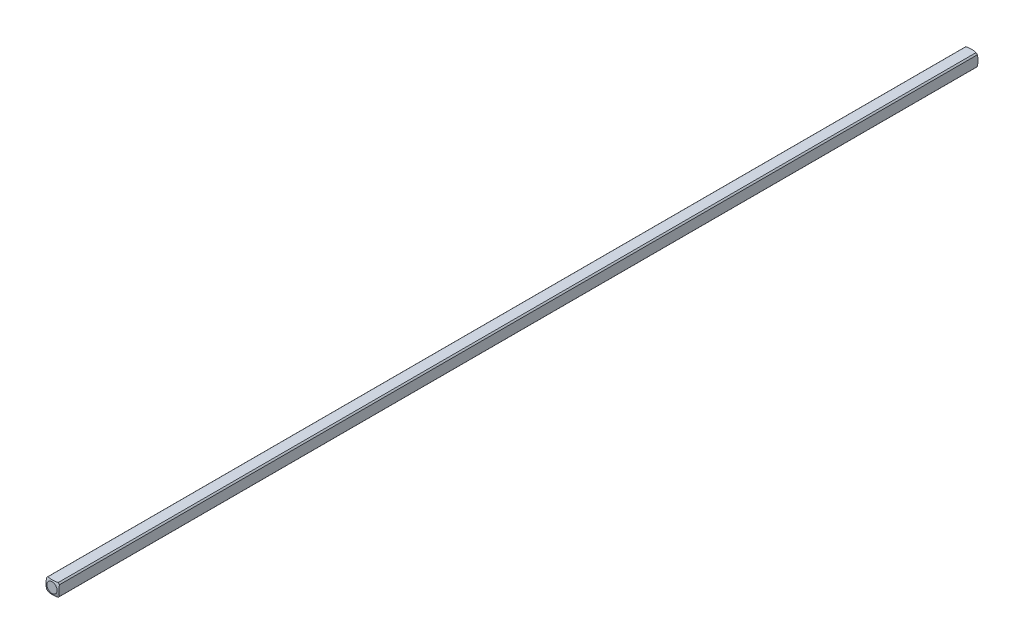
SolidWorks part; units mm, degrees
material "Custom Plastic"
ref_plane "Front Plane" through (0, 0, 0) normal (0, 0, 1) x (1, 0, 0)
ref_plane "Top Plane" through (0, 0, 0) normal (0, 1, 0) x (1, 0, 0)
ref_plane "Right Plane" through (0, 0, 0) normal (1, 0, 0) x (0, 0, -1)
sketch "Sketch1" plane through (0, 0, 0) normal (0, 0, 1) x (1, 0, 0)
  line L0 (-1.5875, -1.5875) -> (1.5875, 1.5875) construction
  line L1 (-1.5875, -1.5875) -> (1.5875, -1.5875)
  line L2 (-1.5875, -1.5875) -> (-1.5875, 1.5875)
  line L3 (-1.5875, 1.5875) -> (1.5875, 1.5875)
  line L4 (1.5875, -1.5875) -> (1.5875, 1.5875)
  dimension "D1" = 3.175
extrude "Boss-Extrude1" add sketch "Sketch1" along normal blind 114.3
sketch "Sketch2" plane through (0, 0, 0) normal (0, 0, -1) x (-1, 0, 0)
  circle A0 centre (0, 0) radius 2.032
  dimension "D1" = 4.064
extrude "Cut-Extrude1" cut sketch "Sketch2" against normal through all flip side to cut
ref_axis "Axis1" through (0, 0, 114.3) along (0, 0, -1)
sketch "Sketch3" plane through (0, 0, 0) normal (0, 1, 0) x (1, 0, 0)
  line L1 (-5.0537, -4.4027) -> (-5.0537, 5.7405)
  line L2 (-5.0537, 5.7405) -> (0, 5.7405)
  line L5 (0, -114.3) -> (0, 0) construction
  line L8 (0, 0.1609) -> (0, 5.7405)
  arc A0 (-5.0537, -4.4027) -> (0, 0.1609) centre (0, -4.9191) cw
  dimension "D1" = 5.08
revolve "Cut-Revolve1" cut sketch "Sketch3" angle 360 about axis through (0, 0, 114.3) along (0, 0, -1)
mirror "Mirror1" about plane through (0, 0, 114.3) normal (0, 0, -1) of bodies 103
